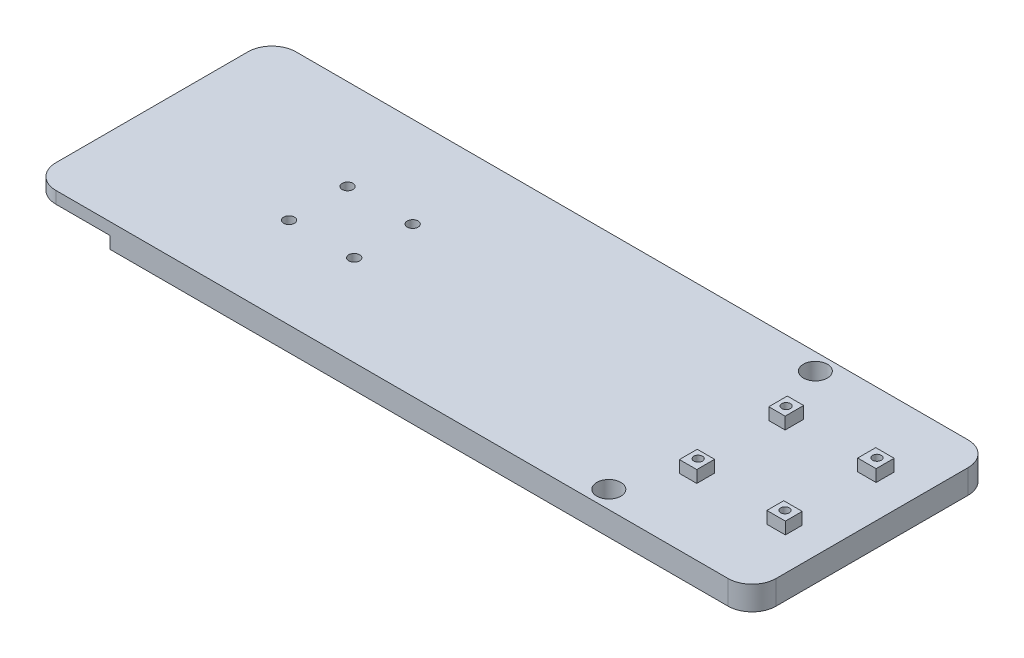
SolidWorks part; units mm, degrees
ref_plane "Front Plane" through (0, 0, 0) normal (0, 0, 1) x (1, 0, 0)
ref_plane "Top Plane" through (0, 0, 0) normal (0, 1, 0) x (1, 0, 0)
ref_plane "Right Plane" through (0, 0, 0) normal (1, 0, 0) x (0, 0, -1)
sketch "Sketch2" plane through (0, 0, 0) normal (0, 1, 0) x (1, 0, 0)
  line L1 (-119.0036, 64.832) -> (180.9964, 64.832)
  line L2 (-119.0036, 64.832) -> (-119.0036, -35.168)
  line L3 (-119.0036, -35.168) -> (180.9964, -35.168)
  line L4 (180.9964, 64.832) -> (180.9964, -35.168)
  dimension "D1" = 300
  dimension "D2" = 100
extrude "Boss-Extrude1" add sketch "Sketch2" along normal blind 10
sketch "Sketch3" plane through (0, 0, 35.168) normal (0, 0, 1) x (1, 0, 0)
  line L0 (-119.0036, 0) -> (-54.0418, 0)
  line L1 (-119.0036, 0) -> (180.9964, 0) construction
  line L2 (-54.0418, 0) -> (-54.0418, 10)
  line L3 (-119.0036, 10) -> (180.9964, 10) construction
  line L4 (-54.0418, 10) -> (-119.0036, 10)
  line L5 (-119.0036, 10) -> (-119.0036, 0)
  line L6 (-86.5227, 0) -> (-86.5227, 5)
  line L7 (-86.5227, 5) -> (-119.0036, 5)
  line M9 (-119.0036, 0) -> (180.9964, 0)
extrude "Cut-Extrude4" cut sketch "Sketch3" against normal blind 100 contours L6 L7 L5 M9
fillet "Fillet2" radius 10 2 edges at (180.9964, 5, -64.832) (180.9964, 5, 35.168)
fillet "Fillet3" radius 10 2 edges at (-119.0036, 7.5, -64.832) (-119.0036, 7.5, 35.168)
sketch "Sketch6" plane through (0, 10, 0) normal (0, 1, 0) x (1, 0, 0)
  line L1 (-109.0036, -35.168) -> (170.9964, -35.168) construction
  line L2 (166.641, -35.168) -> (166.641, -6.0234)
  line L3 (170.9964, 64.832) -> (-109.0036, 64.832) construction
  line L6 (166.641, -35.168) -> (166.641, -6.0234)
  line L7 (166.641, 64.832) -> (166.641, 36.9766)
  line L8 (166.641, 36.9766) -> (166.641, 64.832)
  line L9 (166.641, 36.9766) -> (166.641, -6.0234)
  line L10 (166.641, -6.0234) -> (123.641, -6.0234)
  line L11 (123.641, -6.0234) -> (123.641, 36.9766)
  line L12 (123.641, 36.9766) -> (166.641, 36.9766)
  line L13 (166.5643, 37.0277) -> (166.7589, -6.0782)
  line L16 (123.4712, -6.0396) -> (123.641, -5.8783)
  line L26 (123.6552, 37.014) -> (125.955, 34.1622)
  line L28 (166.8008, 37.106) -> (163.489, 34.6222)
  line L30 (123.3792, -6.2236) -> (126.507, -3.2798)
  line L31 (166.8008, -5.9476) -> (163.121, -3.4638)
  line L33 (123.7472, 37.014) -> (128.8069, 37.014)
  line L34 (123.7472, 37.014) -> (123.7472, 31.9543)
  line L35 (123.7472, 31.9543) -> (128.8069, 31.9543)
  line L36 (128.8069, 37.014) -> (128.8069, 31.9543)
  line L37 (123.6552, -5.7636) -> (128.8069, -5.7636)
  line L38 (123.6552, -5.7636) -> (123.6552, -0.6119)
  line L39 (123.6552, -0.6119) -> (128.8069, -0.6119)
  line L40 (128.8069, -5.7636) -> (128.8069, -0.6119)
  line L41 (166.8008, -6.1316) -> (160.9131, -6.1316)
  line L42 (166.8008, -6.1316) -> (166.8008, -0.8879)
  line L43 (166.8008, -0.8879) -> (160.9131, -0.8879)
  line L44 (160.9131, -6.1316) -> (160.9131, -0.8879)
  line L45 (166.5248, 36.922) -> (161.4651, 36.922)
  line L46 (166.5248, 36.922) -> (166.5248, 31.8623)
  line L47 (166.5248, 31.8623) -> (161.4651, 31.8623)
  line L48 (161.4651, 36.922) -> (161.4651, 31.8623)
  circle A1 centre (125.9051, 34.1214) radius 1.8
  circle A2 centre (126.5464, -3.164) radius 1.8
  circle A3 centre (163.2821, -3.7137) radius 1.8
  circle A4 centre (163.4654, 34.3962) radius 1.8
  circle A5 centre (125.8359, 34.0432) radius 1.8475
  circle A6 centre (126.5658, -3.1843) radius 1.5961
  circle A7 centre (163.2458, -3.7317) radius 1.7216
  circle A8 centre (163.6108, 34.4994) radius 1.8362
  dimension "D1" = 43
  dimension "D3" = 43
  dimension "D2" = 100
extrude "Cut-Extrude11" cut sketch "Sketch6" against normal blind 100 contours A1 | A2 | A3 | A4
sketch "Sketch10" plane through (0, 10, 0) normal (0, 1, 0) x (1, 0, 0)
  line L1 (121.1463, 39.2522) -> (168.2135, 39.2522)
  line L2 (121.1463, 39.2522) -> (121.1463, -11.0369)
  line L3 (121.1463, -11.0369) -> (168.2135, -11.0369)
  line L4 (168.2135, 39.2522) -> (168.2135, -11.0369)
  line L5 (122.407, 37.9914) -> (129.4111, 37.9914)
  line L6 (122.407, 37.9914) -> (122.407, 30.287)
  line L7 (122.407, 30.287) -> (129.4111, 30.287)
  line L8 (129.4111, 37.9914) -> (129.4111, 30.287)
  line L9 (122.8273, 0.0295) -> (130.2515, 0.0295)
  line L10 (122.8273, 0.0295) -> (122.8273, -7.3948)
  line L11 (122.8273, -7.3948) -> (130.2515, -7.3948)
  line L12 (130.2515, 0.0295) -> (130.2515, -7.3948)
  line L13 (159.5284, 37.8514) -> (167.2329, 37.8514)
  line L14 (159.5284, 37.8514) -> (159.5284, 30.287)
  line L15 (159.5284, 30.287) -> (167.2329, 30.287)
  line L16 (167.2329, 37.8514) -> (167.2329, 30.287)
  line L17 (159.5284, -0.3907) -> (167.2329, -0.3907)
  line L18 (159.5284, -0.3907) -> (159.5284, -7.5348)
  line L19 (159.5284, -7.5348) -> (167.2329, -7.5348)
  line L20 (167.2329, -0.3907) -> (167.2329, -7.5348)
  line L21 (122.5218, 38.0191) -> (129.3223, 38.0191)
  line L22 (122.5218, 38.0191) -> (122.5218, 30.2472)
  line L23 (122.5218, 30.2472) -> (129.3223, 30.2472)
  line L24 (129.3223, 38.0191) -> (129.3223, 30.2472)
  line L25 (122.9536, 0.0231) -> (130.1858, 0.0231)
  line L26 (122.9536, 0.0231) -> (122.9536, -7.533)
  line L27 (122.9536, -7.533) -> (130.1858, -7.533)
  line L28 (130.1858, 0.0231) -> (130.1858, -7.533)
  line L29 (167.4262, -7.533) -> (159.4384, -7.533)
  line L30 (167.4262, -7.533) -> (167.4262, -0.5167)
  line L31 (167.4262, -0.5167) -> (159.4384, -0.5167)
  line L32 (159.4384, -7.533) -> (159.4384, -0.5167)
  line L33 (159.5464, 37.8032) -> (167.2103, 37.8032)
  line L34 (159.5464, 37.8032) -> (159.5464, 30.1392)
  line L35 (159.5464, 30.1392) -> (167.2103, 30.1392)
  line L36 (167.2103, 37.8032) -> (167.2103, 30.1392)
  circle M4 centre (163.4654, 34.3962) radius 1.8
  circle M5 centre (163.2821, -3.7137) radius 1.8
  circle M6 centre (126.5464, -3.164) radius 1.8
  circle M7 centre (125.9051, 34.1214) radius 1.8
extrude "Boss-Extrude3" add sketch "Sketch10" along normal blind 5 contours L24 L5 L22 L7 M7 | L28 L25 L26 L11 M6 | L20 L31 L18 L29 M5 | L36 L33 L34 L15 M4
sketch "Sketch8" plane through (0, 10, 0) normal (0, 1, 0) x (1, 0, 0)
  line L0 (-54.0036, 31.332) -> (-49.6902, 27.0186)
  line L1 (-19.1252, -1.668) -> (-22.5497, 2.6453)
  line L2 (-54.0036, -1.668) -> (-54.0036, 31.332)
  line L3 (-19.1252, 31.332) -> (-22.5497, 27.0186)
  line L5 (-54.0036, 14.832) -> (-54.0036, 31.332)
  line L6 (-54.0036, 14.832) -> (-54.0036, -1.668)
  line L7 (-54.0036, -1.668) -> (-19.1252, -1.668)
  line L8 (-19.1252, -1.668) -> (-19.1252, 31.332)
  line L9 (-19.1252, 31.332) -> (-54.0036, 31.332)
  line L10 (-54.0036, -1.668) -> (-49.6902, 2.6453)
  circle A0 centre (-49.6902, 27.0186) radius 2.25
  circle A1 centre (-49.6902, 2.6453) radius 2.25
  circle A2 centre (-22.5497, 27.0186) radius 2.25
  circle A3 centre (-22.5497, 2.6453) radius 2.25
sketch "Sketch11" plane through (0, 10, 0) normal (0, 1, 0) x (1, 0, 0)
  circle A0 centre (114.3793, 57.8155) radius 5.0077
  circle A1 centre (113.9865, -27.8221) radius 5.0077
extrude "Cut-Extrude13" cut sketch "Sketch11" against normal blind 30
sketch "Croquis2" plane through (0, 0, 0) normal (0, -1, 0) x (1, 0, 0)
  line L0 (-54.0036, 1.668) -> (-19.1252, 1.668) construction
  line L5 (-26.2355, 1.668) -> (-19.1252, 1.668)
  line L6 (-26.2355, 1.668) -> (-26.2355, -31.332)
  line L7 (-26.2355, -31.332) -> (-19.1252, -31.332)
  line L8 (-19.1252, 1.668) -> (-19.1252, -31.332)
  line L9 (-19.1252, -31.332) -> (-54.0036, -31.332) construction
  line L10 (-54.0036, 1.668) -> (-45.8756, 1.668)
  line L11 (-54.0036, 1.668) -> (-54.0036, -31.332)
  line L12 (-54.0036, -31.332) -> (-45.8756, -31.332)
  line L13 (-45.8756, 1.668) -> (-45.8756, -31.332)
  dimension "D1" = 33
extrude "Saliente-Extruir1" add sketch "Croquis2" along normal blind 15
extrude "Cortar-Extruir1" cut sketch "Sketch8" against normal blind 50
